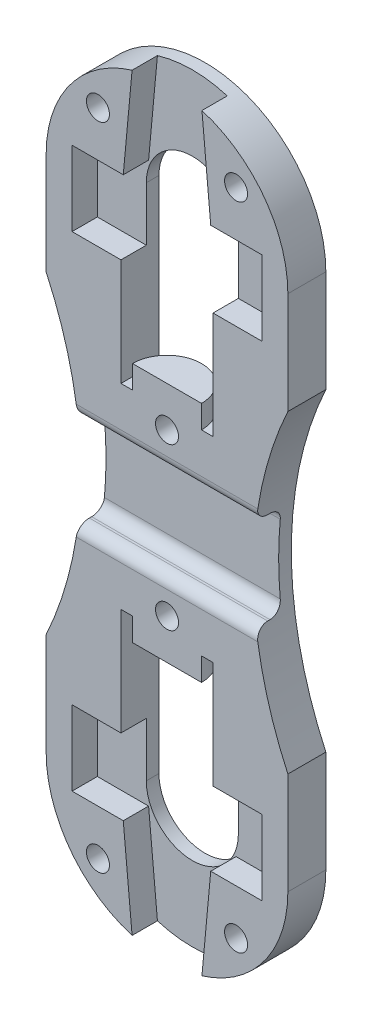
SolidWorks part; units mm, degrees
material "普通碳钢"
ref_plane "前视基准面" through (0, 0, 0) normal (0, 0, 1) x (1, 0, 0)
ref_plane "上视基准面" through (0, 0, 0) normal (0, 1, 0) x (1, 0, 0)
ref_plane "右视基准面" through (0, 0, 0) normal (1, 0, 0) x (0, 0, -1)
sketch "草图1" plane through (0, 0, 0) normal (0, 0, 1) x (1, 0, 0)
  line L0 (0, 0) -> (0, 22.5) construction
  line L1 (10.5, -13.6382) -> (10.5, -22.5)
  line L2 (-10.5, 22.5) -> (-10.5, 13.6382)
  line L3 (-4, -22.5) -> (-4, -8.5)
  line L4 (10.5, 22.5) -> (10.5, 13.6382)
  line L5 (-10.5, -13.6382) -> (-10.5, -22.5)
  line L6 (4, -22.5) -> (4, -8.5)
  line L7 (0, 0) -> (40, 0) construction
  line L8 (-4, 22.5) -> (-4, 8.5)
  line L9 (-4, 8.5) -> (4, 8.5)
  line L10 (4, 22.5) -> (4, 8.5)
  line L11 (-4, -8.5) -> (4, -8.5)
  arc A0 (10.5, 22.5) -> (-10.5, 22.5) centre (0, 22.5) ccw
  arc A1 (10.5, -22.5) -> (-10.5, -22.5) centre (0, -22.5) cw
  arc A2 (10.5, 13.6382) -> (10.5, -13.6382) centre (40, 0) ccw
  arc A3 (-10.5, 13.6382) -> (-10.5, -13.6382) centre (-40, 0) cw
  arc A4 (4, 22.5) -> (-4, 22.5) centre (0, 22.5) ccw
  arc A5 (4, -22.5) -> (-4, -22.5) centre (0, -22.5) cw
  circle A6 centre (0, 7) radius 1
  circle A7 centre (0, -7) radius 1
  circle A8 centre (-6, 28.25) radius 1
  circle A9 centre (6, 28.25) radius 1
  circle A10 centre (6, -28.25) radius 1
  circle A11 centre (-6, -28.25) radius 1
  point P0 (0, 0)
  point P15 (0, 26.5)
  point P16 (0, 19.246)
  point P21 (-4, 15.5)
  point P22 (4, 15.5)
  dimension "D3" = 21
  dimension "D2" = 65
  dimension "D6" = 8
  dimension "D9" = 2
  dimension "D11" = 2
  dimension "D1" = 21
  dimension "D4" = 45
  dimension "D5" = 40
  dimension "D7" = 8
  dimension "D8" = 18
  dimension "D10" = 14
  dimension "D12" = 12
  dimension "D13" = 56.5
extrude "凸台-拉伸1" add sketch "草图1" along normal blind 3.3
sketch "草图2" plane through (0, 0, 3.3) normal (0, 0, 1) x (1, 0, 0)
  line L0 (-3.8, 24.3) -> (-2.8714, 34.3)
  line L1 (-8.25, 24.3) -> (-3.8, 24.3)
  line L2 (-8.25, 24.3) -> (-8.25, 17.8)
  line L3 (-8.25, 17.8) -> (8.25, 17.8)
  line L4 (8.25, 24.3) -> (8.25, 17.8)
  line L5 (-8.25, 24.3) -> (8.25, 17.8) construction
  line L6 (-8.25, 17.8) -> (8.25, 24.3) construction
  line L7 (-2.8714, 34.3) -> (2.8714, 34.3)
  line L8 (0, 21.05) -> (0, 34.3) construction
  line L9 (3.8, 24.3) -> (2.8714, 34.3)
  line L10 (3.8, 24.3) -> (8.25, 24.3)
  line L11 (0, 0) -> (16.8737, 0) construction
  line L12 (-10, 4) -> (10, 4)
  line L13 (-10, 4) -> (-10, -4)
  line L14 (-10, -4) -> (10, -4)
  line L15 (10, 4) -> (10, -4)
  line L16 (-10, 4) -> (10, -4) construction
  line L17 (-10, -4) -> (10, 4) construction
  line L18 (3.8, -24.3) -> (8.25, -24.3)
  line L19 (8.25, -24.3) -> (8.25, -17.8)
  line L20 (-8.25, -17.8) -> (8.25, -17.8)
  line L21 (-8.25, -24.3) -> (-8.25, -17.8)
  line L22 (-8.25, -24.3) -> (-3.8, -24.3)
  line L23 (-3.8, -24.3) -> (-2.8714, -34.3)
  line L24 (-2.8714, -34.3) -> (2.8714, -34.3)
  line L25 (3.8, -24.3) -> (2.8714, -34.3)
  arc A0 (4, 22.5) -> (-4, 22.5) centre (0, 22.5) ccw construction
  point P0 (0, 21.05)
  point P12 (0, 0)
  dimension "D1" = 6.5
  dimension "D2" = 16.5
  dimension "D3" = 3.8
  dimension "D4" = 10.61
  dimension "D5" = 10
  dimension "D6" = 8
  dimension "D7" = 20
  dimension "D8" = 1.45
extrude "切除-拉伸1" cut sketch "草图2" against normal blind 2.2
fillet "圆角1" radius 1 4 edges at (0, 4, 1.1) (0, 4, 3.3) (0, -4, 1.1) (0, -4, 3.3)
sketch "草图3" plane through (0, 8.5, 0) normal (0, 1, 0) x (1, 0, 0)
  line L0 (-4, -3.3) -> (4, -3.3) construction
  line L1 (-3, -3.3) -> (3, -3.3)
  arc A0 (3, -3.3) -> (-3, -3.3) centre (0, -3.3) ccw
  dimension "D1" = 6
extrude "凸台-拉伸2" add sketch "草图3" along normal blind 2
mirror "镜向1" about plane through (0, 0, 0) normal (0, 1, 0) of "凸台-拉伸2"
sketch "草图4" plane through (0, 0, 1.1) normal (0, 0, 1) x (1, 0, 0)
  line L0 (0, 18.5699) -> (0, 24.5699) construction
  line L1 (-4, 18.5699) -> (-4, 24.5699)
  line L2 (4, 18.5699) -> (4, 24.5699)
  line L3 (0, 0) -> (16.5873, 0) construction
  line L4 (0, -18.5699) -> (0, -24.5699) construction
  line L5 (-4, -18.5699) -> (-4, -24.5699)
  line L6 (4, -18.5699) -> (4, -24.5699)
  arc A0 (-4, 18.5699) -> (4, 18.5699) centre (0, 18.5699) ccw
  arc A1 (4, 24.5699) -> (-4, 24.5699) centre (0, 24.5699) ccw
  arc A2 (-4, -18.5699) -> (4, -18.5699) centre (0, -18.5699) cw
  arc A3 (4, -24.5699) -> (-4, -24.5699) centre (0, -24.5699) cw
  point P3 (0, 21.5699)
  point P12 (0, -21.5699)
  dimension "D1" = 4
  dimension "D2" = 3
